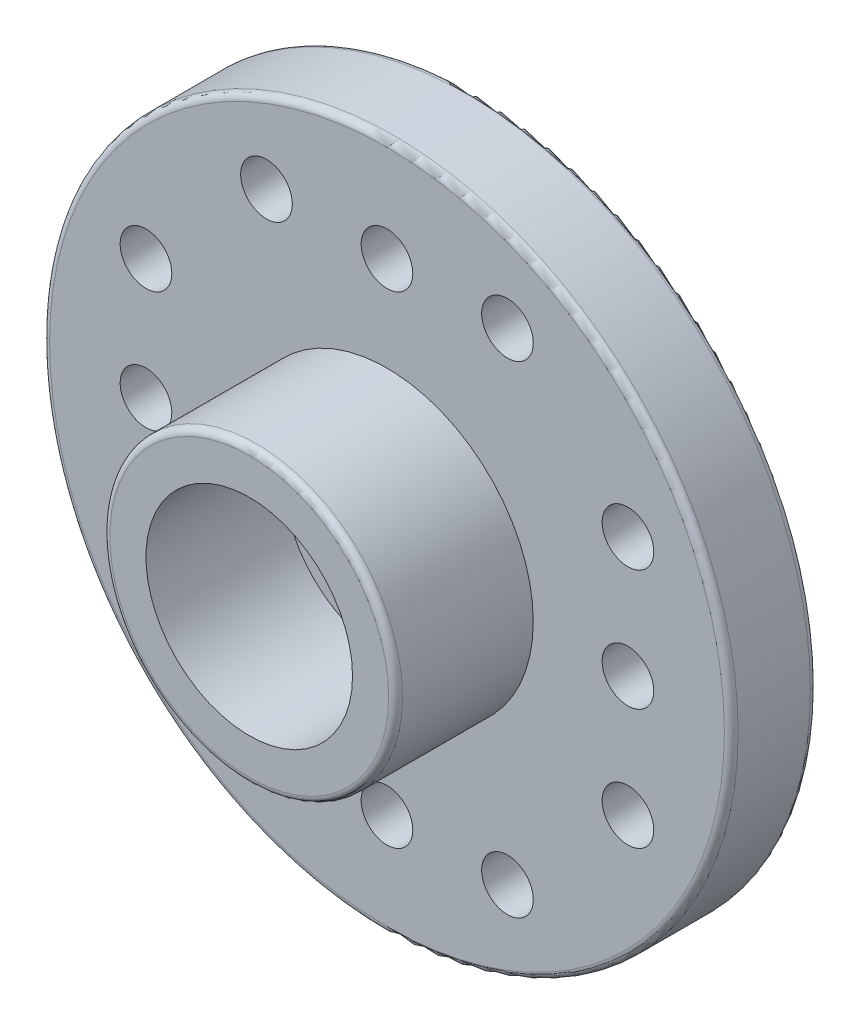
SolidWorks part; units mm, degrees
ref_plane "Front Plane" through (0, 0, 0) normal (0, 0, 1) x (1, 0, 0)
ref_plane "Top Plane" through (0, 0, 0) normal (0, 1, 0) x (1, 0, 0)
ref_plane "Right Plane" through (0, 0, 0) normal (1, 0, 0) x (0, 0, -1)
sketch "Sketch1" plane through (0, 0, 0) normal (0, 0, 1) x (1, 0, 0)
  line L0 (-7, 3.5) -> (-7, -3.5) construction
  line L1 (-7, 0) -> (0, 0) construction
  circle A0 centre (0, 0) radius 10
  circle A1 centre (-7, 0) radius 0.75
  circle A2 centre (3.5, 7) radius 0.75
  circle A3 centre (0, 7) radius 0.75
  circle A4 centre (-3.5, 7) radius 0.75
  circle A5 centre (7, -3.5) radius 0.75
  circle A6 centre (7, 0) radius 0.75
  circle A7 centre (7, 3.5) radius 0.75
  circle A8 centre (-3.5, -7) radius 0.75
  circle A9 centre (0, -7) radius 0.75
  circle A10 centre (3.5, -7) radius 0.75
  circle A11 centre (-7, -3.5) radius 0.75
  circle A13 centre (-7, 3.5) radius 0.75
  circle A22 centre (0, 0) radius 1.5
  point P25 (0, 0)
  dimension "D2" = 20
  dimension "D4" = 7
  dimension "D5" = 3.5
  dimension "D14" = 3
  dimension "D6" = 3.5
  dimension "D3" = 1.5
extrude "Boss-Extrude1" add sketch "Sketch1" along normal blind 2.5
sketch "Sketch5" plane through (0, 0, 2.5) normal (0, 0, 1) x (1, 0, 0)
  circle A0 centre (0, 0) radius 3
  circle A1 centre (0, 0) radius 4.25
  dimension "D1" = 8.5
extrude "Boss-Extrude2" add sketch "Sketch5" along normal blind 4
sketch "Sketch6" plane through (0, 0, 0) normal (0, 0, -1) x (-1, 0, 0)
  circle A0 centre (0, 0) radius 4.5
  dimension "D1" = 9
extrude "Cut-Extrude1" cut sketch "Sketch6" against normal blind 0.8
sketch "Sketch7" plane through (0, 0, 0.8) normal (0, 0, -1) x (-1, 0, 0)
  circle A0 centre (0.1627, 0) radius 3.5
  circle A1 centre (0.1627, 0) radius 3.7
  dimension "D1" = 7
  dimension "D2" = 0.2
extrude "Boss-Extrude3" add sketch "Sketch7" along normal up to surface (0.8 mm away) up to face at (-4.5, 0, 0)
fillet "Fillet1" radius 0.2 4 edges at (10, 0, 0) (10, 0, 2.5) (-4.5, 0, 0) (4.25, 0, 6.5)
